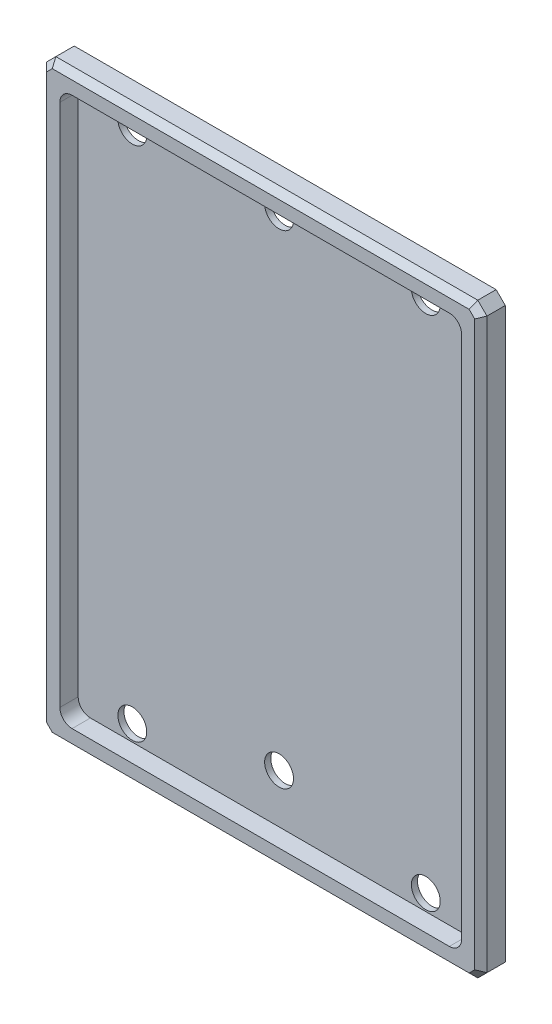
SolidWorks part; units mm, degrees
material "AISI 304"
ref_plane "Front Plane" through (0, 0, 0) normal (0, 0, 1) x (1, 0, 0)
ref_plane "Top Plane" through (0, 0, 0) normal (0, 1, 0) x (1, 0, 0)
ref_plane "Right Plane" through (0, 0, 0) normal (1, 0, 0) x (0, 0, -1)
sketch "Sketch1" plane through (0, 0, 0) normal (0, 0, 1) x (1, 0, 0)
  line L1 (114.3, -152.4) -> (-114.3, -152.4)
  line L2 (114.3, -152.4) -> (114.3, 152.4)
  line L3 (114.3, 152.4) -> (-114.3, 152.4)
  line L4 (-114.3, -152.4) -> (-114.3, 152.4)
  line L5 (114.3, -152.4) -> (-114.3, 152.4) construction
  line L6 (114.3, 152.4) -> (-114.3, -152.4) construction
  point P0 (0, 0)
  dimension "D1" = 228.6
  dimension "D2" = 304.8
extrude "Boss-Extrude1" add sketch "Sketch1" along normal blind 12.7
sketch "Sketch2" plane through (0, 0, 12.7) normal (0, 0, 1) x (1, 0, 0)
  line L0 (-114.3, 152.4) -> (-114.3, -152.4) construction
  line L1 (97.95, -142.4) -> (-97.95, -142.4)
  line L2 (104.3, -136.05) -> (104.3, 136.05)
  line L3 (97.95, 142.4) -> (-97.95, 142.4)
  line L4 (-104.3, -136.05) -> (-104.3, 136.05)
  line L5 (104.3, -142.4) -> (-104.3, 142.4) construction
  line L6 (104.3, 142.4) -> (-104.3, -142.4) construction
  line L7 (114.3, 152.4) -> (-114.3, 152.4) construction
  arc A0 (-97.95, -142.4) -> (-104.3, -136.05) centre (-97.95, -136.05) cw
  arc A1 (97.95, -142.4) -> (104.3, -136.05) centre (97.95, -136.05) ccw
  arc A2 (104.3, 136.05) -> (97.95, 142.4) centre (97.95, 136.05) ccw
  arc A3 (-97.95, 142.4) -> (-104.3, 136.05) centre (-97.95, 136.05) ccw
  point P0 (0, 0)
  dimension "D3" = 6.35
  dimension "D1" = 10
  dimension "D2" = 10
extrude "Cut-Extrude1" cut sketch "Sketch2" against normal blind 9.525
sketch "Sketch4" plane through (0, 0, 3.175) normal (0, 0, 1) x (1, 0, 0)
  line L0 (-97.95, -142.4) -> (97.95, -142.4) construction
  line L1 (97.95, 142.4) -> (-97.95, 142.4) construction
  line L4 (-114.3, 152.4) -> (-114.3, -152.4) construction
  line L5 (114.3, -152.4) -> (114.3, 152.4) construction
  line L8 (-97.95, -142.4) -> (97.95, -142.4) construction
  circle A0 centre (-76.2, 134.05) radius 7.5
  circle A1 centre (76.2, 134.05) radius 7.5
  circle A2 centre (-76.2, -134.05) radius 7.5
  circle A3 centre (76.2, -134.05) radius 7.5
  circle A4 centre (0, 134.05) radius 7.5
  circle A5 centre (0, -117) radius 7.5
  dimension "D1" = 15
  dimension "D2" = 15
  dimension "D3" = 15
  dimension "D4" = 15
  dimension "D13" = 15
  dimension "D14" = 15
  dimension "D15" = 8.35
  dimension "D5" = 0
  dimension "D6" = 38.1
  dimension "D7" = 38.1
  dimension "D8" = 0
  dimension "D9" = 8.35
  dimension "D10" = 38.1
  dimension "D11" = 38.1
  dimension "D16" = 25.4
extrude "Cut-Extrude2" cut sketch "Sketch4" against normal through all
hole_wizard "M4x0.7 Tapped Hole1" positions "Sketch8" profile "Sketch9" tap size "M4x0.7" standard "ANSI Metric"
sketch "Sketch8" plane through (0, 0, 0) normal (0, 0, -1) x (-1, 0, 0)
  line L0 (114.3, -152.4) -> (-114.3, -152.4) construction
  line L1 (-114.3, -152.4) -> (-114.3, 152.4) construction
  point P0 (-109.3, -102.4)
  point P2 (-109.3, 0)
  point P4 (-109.3, 113.6)
  point P14 (-114.3, 0)
  dimension "D1" = 266
  dimension "D2" = 5
  dimension "D3" = 50
sketch "Sketch9" plane through (109.3, -102.4, 0) normal (1, 0, 0) x (0, 1, 0)
  line L0 (0, 0) -> (0, 8.9914)
  line L1 (0, 8.9914) -> (1.65, 8)
  line L2 (1.65, 8) -> (1.65, 0)
  line L5 (1.65, 0) -> (0, 0)
  line L10 (0, 8.9914) -> (-1.65, 8) construction
  line L11 (0, -6.35) -> (0, 107.95) construction
  dimension "Tap Drill Dia." = 3.3
  dimension "Tap Drill Depth" = 8
  dimension "Drill Angle" = 118
cosmetic thread "Hole Thread1" parameters "D1"=6, "D2"=4
cosmetic thread "Hole Thread2" parameters "D1"=6, "D2"=4
cosmetic thread "Hole Thread3" parameters "D1"=6, "D2"=4
chamfer "Chamfer1" distance 4.7625 angle 45 4 edges at (-114.3, -152.4, 6.35) (114.3, -152.4, 6.35) (-114.3, 152.4, 6.35) (114.3, 152.4, 6.35)
chamfer "Chamfer2" distance 3.175 angle 45 8 edges at (-111.9188, 150.0187, 12.7) (0, 152.4, 12.7) (111.9187, 150.0187, 12.7) (114.3, 0, 12.7) (111.9187, -150.0188, 12.7) (0, -152.4, 12.7) (-111.9188, -150.0188, 12.7) (-114.3, 0, 12.7)
